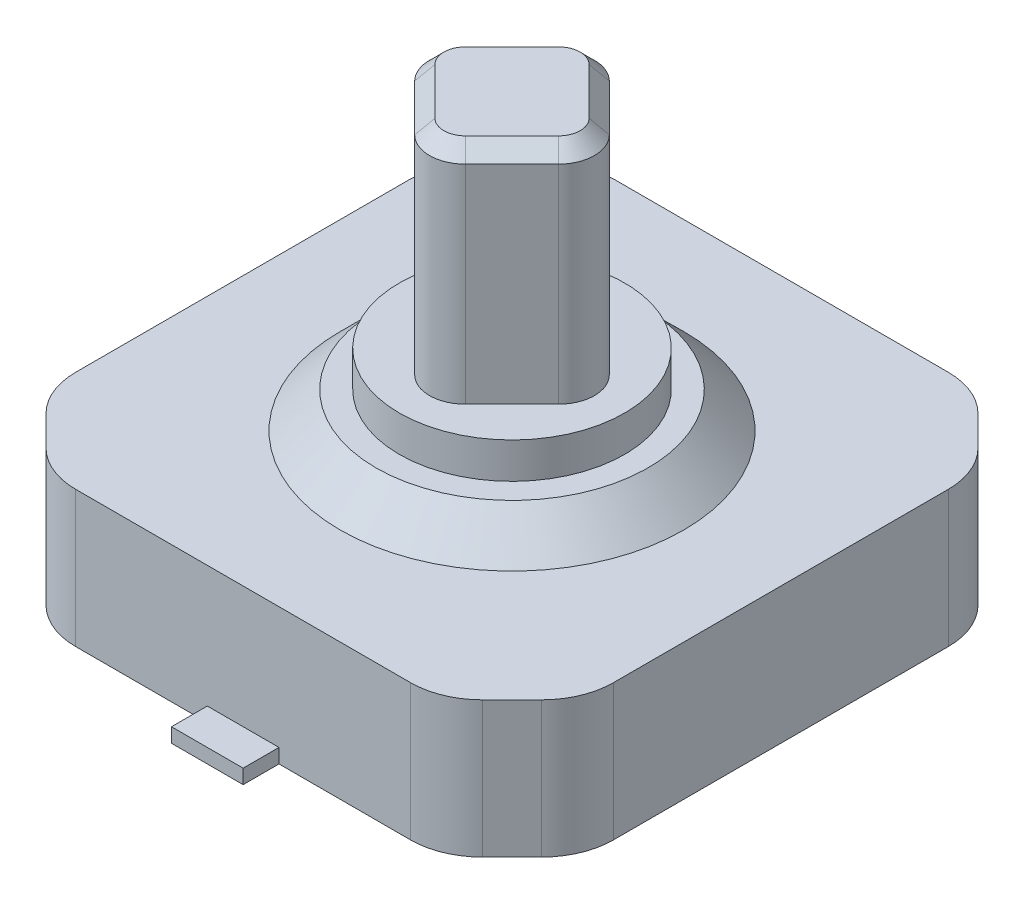
SolidWorks part; units mm, degrees
ref_plane "Спереди" through (0, 0, 0) normal (0, 0, 1) x (1, 0, 0)
ref_plane "Сверху" through (0, 0, 0) normal (0, 1, 0) x (1, 0, 0)
ref_plane "Справа" through (0, 0, 0) normal (1, 0, 0) x (0, 0, -1)
other "Configuration Table"
sketch "Sketch1" plane through (0, 0, 0) normal (0, 1, 0) x (1, 0, 0)
  line L0 (-3.4571, 3.0429) -> (-3.0429, 3.4571)
  line L1 (-2.3358, -3.75) -> (2.3358, -3.75)
  line L2 (-3.75, -2.3358) -> (-3.75, 2.3358)
  line L3 (-2.3358, 3.75) -> (2.3358, 3.75)
  line L4 (3.75, -2.3358) -> (3.75, 2.3358)
  line L5 (-3.75, -3.75) -> (3.75, 3.75) construction
  line L6 (-3.75, 3.75) -> (3.75, -3.75) construction
  line L7 (3.0429, 3.4571) -> (3.4571, 3.0429)
  line L8 (3.0429, -3.4571) -> (3.4571, -3.0429)
  line L9 (-3.4571, -3.0429) -> (-3.0429, -3.4571)
  arc A0 (3.0429, 3.4571) -> (2.3358, 3.75) centre (2.3358, 2.75) ccw
  arc A1 (3.4571, 3.0429) -> (3.75, 2.3358) centre (2.75, 2.3358) cw
  arc A2 (3.4571, -3.0429) -> (3.75, -2.3358) centre (2.75, -2.3358) ccw
  arc A3 (3.0429, -3.4571) -> (2.3358, -3.75) centre (2.3358, -2.75) cw
  arc A4 (-3.0429, -3.4571) -> (-2.3358, -3.75) centre (-2.3358, -2.75) ccw
  arc A5 (-3.4571, -3.0429) -> (-3.75, -2.3358) centre (-2.75, -2.3358) cw
  arc A6 (-3.4571, 3.0429) -> (-3.75, 2.3358) centre (-2.75, 2.3358) ccw
  arc A7 (-3.0429, 3.4571) -> (-2.3358, 3.75) centre (-2.3358, 2.75) cw
  point P0 (0, 0)
  dimension "D1" = 1
extrude "Boss-Extrude1" add sketch "Sketch1" along normal blind 1.9
sketch "Sketch2" plane through (0, 0, 0) normal (0, 1, 0) x (1, 0, 0)
  line L1 (0.3536, -1.0041) -> (1.0041, -0.3536)
  line L2 (-0.3536, -1.0041) -> (-1.0041, -0.3536)
  line L3 (-1.0041, 0.3536) -> (-0.3536, 1.0041)
  line L4 (1.0041, 0.3536) -> (0.3536, 1.0041)
  line L5 (0, -1.3576) -> (0, 1.3576) construction
  line L6 (-1.3576, 0) -> (1.3576, 0) construction
  arc A0 (0.3536, -1.0041) -> (-0.3536, -1.0041) centre (0, -0.6505) cw
  arc A1 (1.0041, -0.3536) -> (1.0041, 0.3536) centre (0.6505, 0) ccw
  arc A2 (-0.3536, 1.0041) -> (0.3536, 1.0041) centre (0, 0.6505) cw
  arc A3 (-1.0041, -0.3536) -> (-1.0041, 0.3536) centre (-0.6505, 0) cw
  point P0 (0, 0)
extrude "Boss-Extrude2" add sketch "Sketch2" along normal blind 6
sketch "Sketch3" plane through (0, 1.9, 0) normal (0, 1, 0) x (1, 0, 0)
  circle A0 centre (0, 0) radius 2.3971
extrude "Boss-Extrude3" add sketch "Sketch3" along normal blind 0.5 draft 45
sketch "Sketch4" plane through (0, 2.4, 0) normal (0, 1, 0) x (1, 0, 0)
  circle A0 centre (0, 0) radius 1.5717
extrude "Boss-Extrude4" add sketch "Sketch4" along normal blind 0.5
sketch "Sketch5" plane through (0, 0, 0) normal (0, 1, 0) x (1, 0, 0)
  line L0 (-2.3358, -3.75) -> (2.3358, -3.75) construction
  line L1 (-0.5, -4.25) -> (0.5, -4.25)
  line L2 (-0.5, -4.25) -> (-0.5, -3.75)
  line L4 (0.5, -4.25) -> (0.5, -3.75)
  line L6 (-0.5, 3.75) -> (0.5, 3.75)
  line L7 (-0.5, -3.75) -> (0.5, -3.75)
  line L8 (0.5, 4.25) -> (0.5, 3.75)
  line L9 (-0.5, 4.25) -> (-0.5, 3.75)
  line L10 (-0.5, 4.25) -> (0.5, 4.25)
  point P0 (0, -3.75)
  point P14 (0, 3.75)
extrude "Boss-Extrude5" add sketch "Sketch5" along normal blind 0.2
chamfer "Chamfer1" distance 0.2 angle 45 8 edges at (-0.6788, 6, 0.6788) (-1.1505, 6, 0) (-0.6788, 6, -0.6788) (0, 6, -1.1505) (0.6788, 6, -0.6788) (1.1505, 6, 0) (0.6788, 6, 0.6788) (0, 6, 1.1505)
